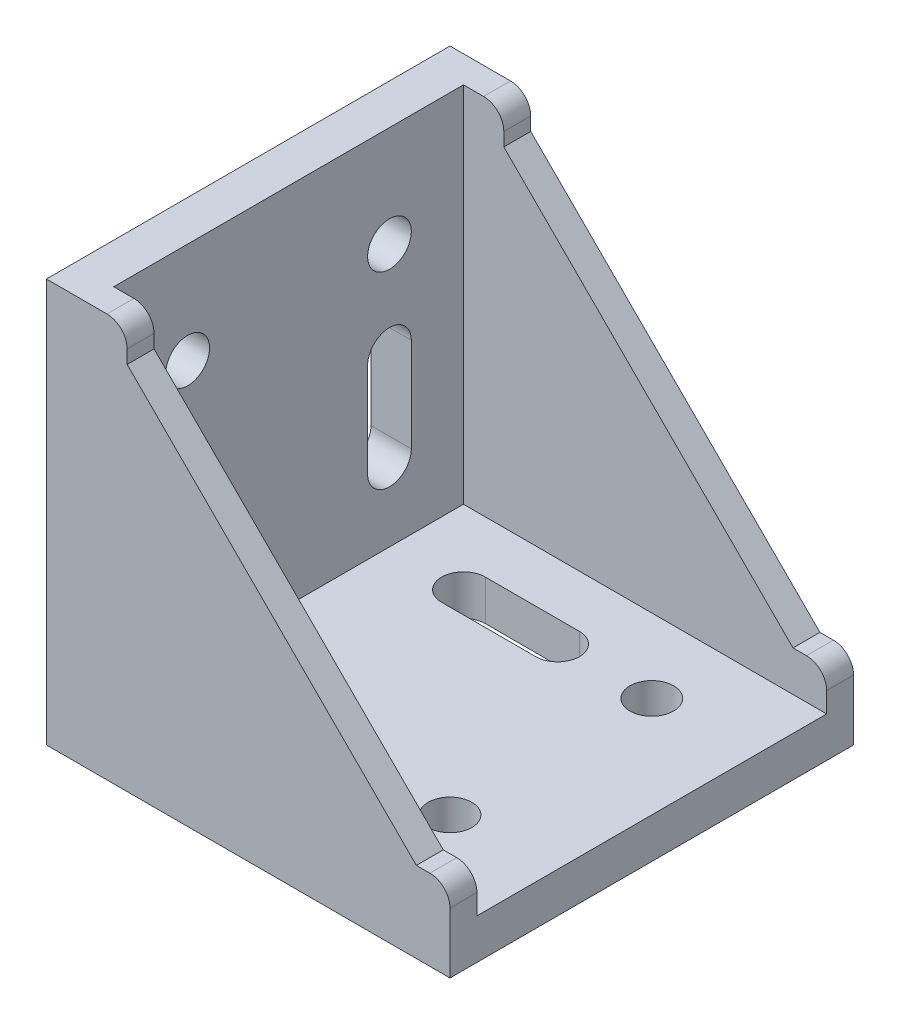
SolidWorks part; units mm, degrees
material "Алюминиевый сплав"
ref_plane "Спереди" through (0, 0, 0) normal (0, 0, 1) x (1, 0, 0)
ref_plane "Сверху" through (0, 0, 0) normal (0, 1, 0) x (1, 0, 0)
ref_plane "Справа" through (0, 0, 0) normal (1, 0, 0) x (0, 0, -1)
sketch "Эскиз1" plane through (0, 0, 0) normal (0, 0, 1) x (1, 0, 0)
  line L0 (0, 60) -> (0, 0)
  line L1 (0, 0) -> (60, 0)
  line L2 (60, 0) -> (60, 6)
  line L4 (6, 60) -> (0, 60)
  line L5 (6, 60) -> (6, 6)
  line L6 (6, 6) -> (60, 6)
  dimension "D1" = 60
  dimension "D2" = 6
extrude "Бобышка-Вытянуть1" add sketch "Эскиз1" along normal mid plane 60
sketch "Эскиз2" plane through (0, 0, 30) normal (0, 0, 1) x (1, 0, 0)
  line L1 (60, 6) -> (6, 6)
  line L2 (6, 6) -> (6, 60)
  line L3 (6, 60) -> (9, 60)
  line L4 (12, 57) -> (12, 55)
  line L5 (12, 55) -> (55, 12)
  line L6 (55, 12) -> (57, 12)
  line L7 (60, 9) -> (60, 6)
  arc A0 (57, 12) -> (60, 9) centre (57, 9) cw
  arc A1 (9, 60) -> (12, 57) centre (9, 57) cw
  point P16 (12, 60)
  dimension "D2" = 3
  dimension "D1" = 5
  dimension "D3" = 6
extrude "Бобышка-Вытянуть2" add sketch "Эскиз2" against normal blind 4
mirror "Зеркальное отражение2" about plane through (0, 0, 0) normal (0, 0, 1) of "Бобышка-Вытянуть2"
sketch "Эскиз3" plane through (0, 6, 0) normal (0, 1, 0) x (1, 0, 0)
  line L0 (17, -15) -> (31, -15) construction
  line L1 (17, -11.75) -> (31, -11.75)
  line L2 (17, -18.25) -> (31, -18.25)
  line L5 (60, -26) -> (60, 26) construction
  line L6 (0, 0) -> (60, 0) construction
  line L7 (17, 15) -> (31, 15) construction
  line L8 (17, 11.75) -> (31, 11.75)
  line L9 (17, 18.25) -> (31, 18.25)
  arc A0 (17, -11.75) -> (17, -18.25) centre (17, -15) ccw
  arc A1 (31, -18.25) -> (31, -11.75) centre (31, -15) ccw
  circle A2 centre (45, -15) radius 3.25
  arc A3 (17, 11.75) -> (17, 18.25) centre (17, 15) cw
  arc A4 (31, 18.25) -> (31, 11.75) centre (31, 15) cw
  circle A5 centre (45, 15) radius 3.25
  point P2 (24, -15)
  point P17 (24, 15)
  dimension "D2" = 3.25
  dimension "D3" = 15
  dimension "D4" = 14
  dimension "D5" = 30
  dimension "D1" = 14
extrude "Вырез-Вытянуть1" cut sketch "Эскиз3" against normal through all
sketch "Эскиз4" plane through (0, 0, 0) normal (0, -1, 0) x (1, 0, 0)
  line L0 (0, 30) -> (0, -30) construction
  line L1 (3, -18) -> (5.5, -18)
  line L2 (3, -18) -> (3, -12)
  line L3 (3, -12) -> (5.5, -12)
  line L4 (5.5, -18) -> (5.5, -12)
  line L5 (3, -18) -> (5.5, -12) construction
  line L6 (3, -12) -> (5.5, -18) construction
  line L7 (54.5, -18) -> (57, -18)
  line L8 (54.5, -18) -> (54.5, -12)
  line L9 (54.5, -12) -> (57, -12)
  line L10 (57, -18) -> (57, -12)
  line L11 (54.5, -18) -> (57, -12) construction
  line L12 (54.5, -12) -> (57, -18) construction
  line L13 (60, 30) -> (60, -30) construction
  line L14 (0, 0) -> (60, 0) construction
  line L15 (54.5, 12) -> (57, 18) construction
  line L16 (54.5, 18) -> (57, 12) construction
  line L17 (3, 12) -> (5.5, 18) construction
  line L18 (3, 18) -> (5.5, 12) construction
  line L19 (57, 18) -> (57, 12)
  line L20 (54.5, 12) -> (57, 12)
  line L21 (54.5, 18) -> (54.5, 12)
  line L22 (54.5, 18) -> (57, 18)
  line L23 (5.5, 18) -> (5.5, 12)
  line L24 (3, 12) -> (5.5, 12)
  line L25 (3, 18) -> (3, 12)
  line L26 (3, 18) -> (5.5, 18)
  point P0 (4.25, -15)
  point P5 (55.75, -15)
  point P25 (55.75, 15)
  point P26 (4.25, 15)
  dimension "D1" = 3
  dimension "D2" = 2.5
  dimension "D3" = 6
  dimension "D4" = 3
  dimension "D5" = 24
extrude "Бобышка-Вытянуть3" add sketch "Эскиз4" along normal blind 2.5
ref_plane "Плоскость1" through (0, 0, 0) normal (-0.7071, 0.7071, 0) x (0.7071, 0.7071, 0)
mirror "Зеркальное отражение3" about plane through (0, 0, 0) normal (-0.7071, 0.7071, 0) of "Бобышка-Вытянуть3", "Вырез-Вытянуть1"
